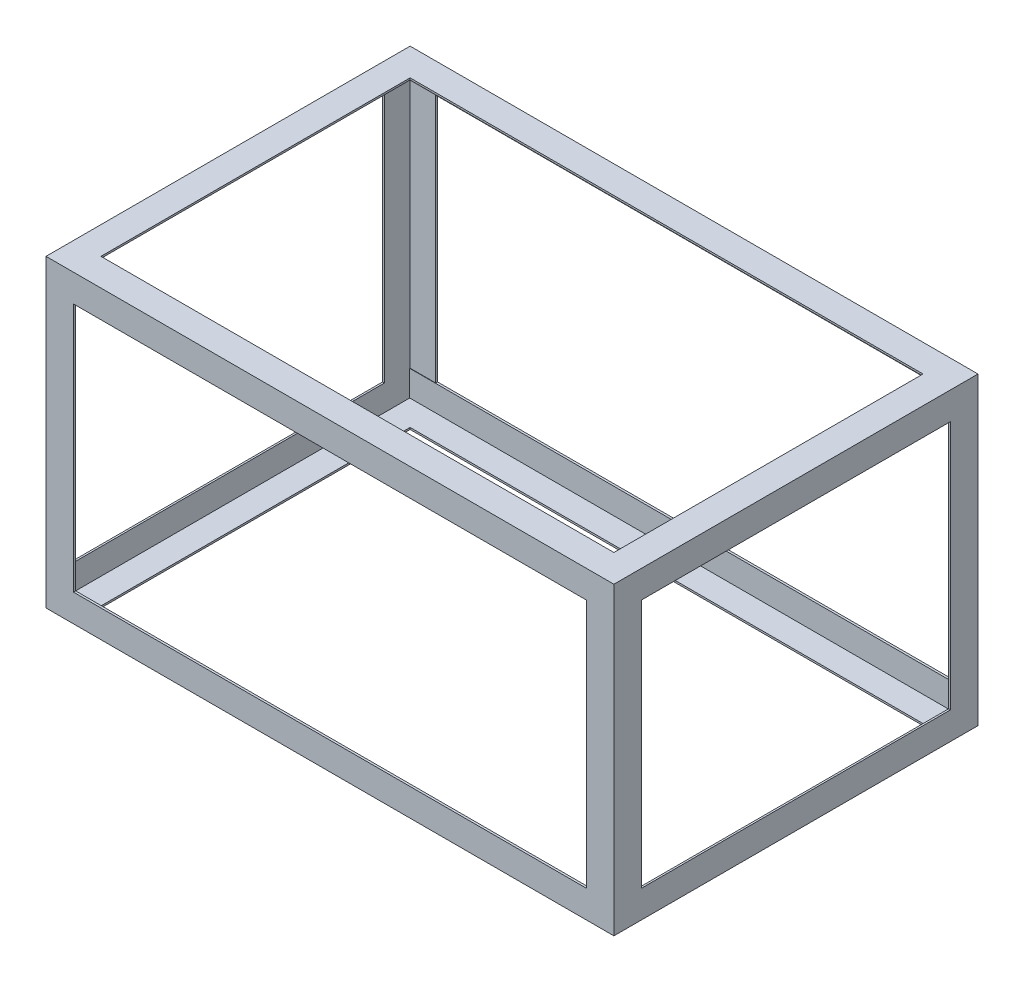
SolidWorks part; units mm, degrees
material "6061 Alloy"
ref_plane "Front Plane" through (0, 0, 0) normal (0, 0, 1) x (1, 0, 0)
ref_plane "Top Plane" through (0, 0, 0) normal (0, 1, 0) x (1, 0, 0)
ref_plane "Right Plane" through (0, 0, 0) normal (1, 0, 0) x (0, 0, -1)
sketch "Sketch2" plane through (0, 0, 0) normal (1, 0, 0) x (0, 0, -1)
  line L0 (-504.825, -346.075) -> (-504.825, -422.275)
  line L1 (504.825, -422.275) -> (-504.825, -422.275) construction
  line L2 (504.825, -422.275) -> (504.825, 422.275) construction
  line L3 (504.825, 422.275) -> (-504.825, 422.275) construction
  line L4 (-504.825, -422.275) -> (-504.825, 422.275) construction
  line L5 (504.825, -422.275) -> (-504.825, 422.275) construction
  line L6 (504.825, 422.275) -> (-504.825, -422.275) construction
  line L7 (-504.825, -422.275) -> (-428.625, -422.275)
  line L8 (-428.625, -422.275) -> (-428.625, -417.195)
  line L9 (-428.625, -417.195) -> (-498.7519, -417.195)
  line L10 (-498.7519, -417.195) -> (-498.7519, -346.075)
  line L11 (-498.7519, -346.075) -> (-504.825, -346.075)
  line L12 (0, 0) -> (0, -148.4726) construction
  line L13 (0, 0) -> (158.633, 0) construction
  line L14 (498.7519, -417.195) -> (498.7519, -346.075)
  line L15 (428.625, -417.195) -> (498.7519, -417.195)
  line L16 (428.625, -422.275) -> (428.625, -417.195)
  line L17 (504.825, -422.275) -> (428.625, -422.275)
  line L18 (504.825, -346.075) -> (504.825, -422.275)
  line L19 (498.7519, -346.075) -> (504.825, -346.075)
  line L20 (428.625, 417.195) -> (498.7519, 417.195)
  line L21 (428.625, 422.275) -> (428.625, 417.195)
  line L22 (504.825, 422.275) -> (428.625, 422.275)
  line L23 (504.825, 346.075) -> (504.825, 422.275)
  line L24 (498.7519, 346.075) -> (504.825, 346.075)
  line L25 (498.7519, 417.195) -> (498.7519, 346.075)
  line L26 (-498.7519, 417.195) -> (-498.7519, 346.075)
  line L27 (-428.625, 417.195) -> (-498.7519, 417.195)
  line L28 (-428.625, 422.275) -> (-428.625, 417.195)
  line L29 (-504.825, 422.275) -> (-428.625, 422.275)
  line L30 (-504.825, 346.075) -> (-504.825, 422.275)
  line L31 (-498.7519, 346.075) -> (-504.825, 346.075)
  point P0 (0, 0)
  dimension "D1" = 1009.65
  dimension "D2" = 844.55
  dimension "D3" = 76.2
  dimension "D4" = 5.08
extrude "Boss-Extrude1" add sketch "Sketch2" along normal blind 1574.8
sketch "Sketch3" plane through (0, 0, 0) normal (0, 0, 1) x (1, 0, 0)
  line L0 (0, -422.275) -> (0, -346.075)
  line L1 (1574.8, -346.075) -> (0, -346.075) construction
  line L2 (0, -346.075) -> (0, -422.275) construction
  line L3 (0, -346.075) -> (5.08, -346.075)
  line L4 (5.08, -346.075) -> (5.08, -417.195)
  line L5 (5.08, -417.195) -> (76.2, -417.195)
  line L6 (76.2, -417.195) -> (76.2, -422.275)
  line L7 (1574.8, -422.275) -> (0, -422.275) construction
  line L8 (76.2, -422.275) -> (0, -422.275)
  line L9 (0, 0) -> (697.1877, 0) construction
  line L10 (787.4, 346.075) -> (787.4, -346.075) construction
  line L11 (1574.8, 346.075) -> (0, 346.075) construction
  line L12 (76.2, 422.275) -> (0, 422.275)
  line L13 (76.2, 417.195) -> (76.2, 422.275)
  line L14 (5.08, 417.195) -> (76.2, 417.195)
  line L15 (5.08, 346.075) -> (5.08, 417.195)
  line L16 (0, 346.075) -> (5.08, 346.075)
  line L17 (0, 422.275) -> (0, 346.075)
  line L18 (1574.8, 422.275) -> (1574.8, 346.075)
  line L19 (1574.8, 346.075) -> (1569.72, 346.075)
  line L20 (1569.72, 346.075) -> (1569.72, 417.195)
  line L21 (1569.72, 417.195) -> (1498.6, 417.195)
  line L22 (1498.6, 417.195) -> (1498.6, 422.275)
  line L23 (1498.6, 422.275) -> (1574.8, 422.275)
  line L24 (1498.6, -422.275) -> (1574.8, -422.275)
  line L25 (1498.6, -417.195) -> (1498.6, -422.275)
  line L26 (1569.72, -417.195) -> (1498.6, -417.195)
  line L27 (1569.72, -346.075) -> (1569.72, -417.195)
  line L28 (1574.8, -346.075) -> (1569.72, -346.075)
  line L29 (1574.8, -422.275) -> (1574.8, -346.075)
  dimension "D1" = 5.08
extrude "Boss-Extrude2" add sketch "Sketch3" along normal up to surface and the other way up to surface
sketch "Sketch4" plane through (0, 422.275, 0) normal (0, 1, 0) x (1, 0, 0)
  line L0 (0, 504.825) -> (0, 428.625)
  line L1 (0, 504.825) -> (0, -504.825) construction
  line L2 (0, 428.625) -> (5.08, 428.625)
  line L3 (5.08, 428.625) -> (5.08, 499.745)
  line L4 (5.08, 499.745) -> (76.2, 499.745)
  line L5 (76.2, 499.745) -> (76.2, 504.825)
  line L6 (0, 504.825) -> (1574.8, 504.825) construction
  line L7 (76.2, 504.825) -> (0, 504.825)
  line L8 (0, 0) -> (1574.8, 0) construction
  line L9 (1574.8, 504.825) -> (1574.8, -504.825) construction
  line L10 (787.4, 0) -> (787.4, 504.825) construction
  line L11 (76.2, -504.825) -> (0, -504.825)
  line L12 (76.2, -499.745) -> (76.2, -504.825)
  line L13 (5.08, -499.745) -> (76.2, -499.745)
  line L14 (5.08, -428.625) -> (5.08, -499.745)
  line L15 (0, -428.625) -> (5.08, -428.625)
  line L16 (0, -504.825) -> (0, -428.625)
  line L17 (1574.8, -504.825) -> (1574.8, -428.625)
  line L18 (1574.8, -428.625) -> (1569.72, -428.625)
  line L19 (1569.72, -428.625) -> (1569.72, -499.745)
  line L20 (1569.72, -499.745) -> (1498.6, -499.745)
  line L21 (1498.6, -499.745) -> (1498.6, -504.825)
  line L22 (1498.6, -504.825) -> (1574.8, -504.825)
  line L23 (1498.6, 504.825) -> (1574.8, 504.825)
  line L24 (1498.6, 499.745) -> (1498.6, 504.825)
  line L25 (1569.72, 499.745) -> (1498.6, 499.745)
  line L26 (1569.72, 428.625) -> (1569.72, 499.745)
  line L27 (1574.8, 428.625) -> (1569.72, 428.625)
  line L28 (1574.8, 504.825) -> (1574.8, 428.625)
  dimension "D1" = 5.08
  dimension "D2" = 76.2
extrude "Boss-Extrude3" add sketch "Sketch4" against normal through all
